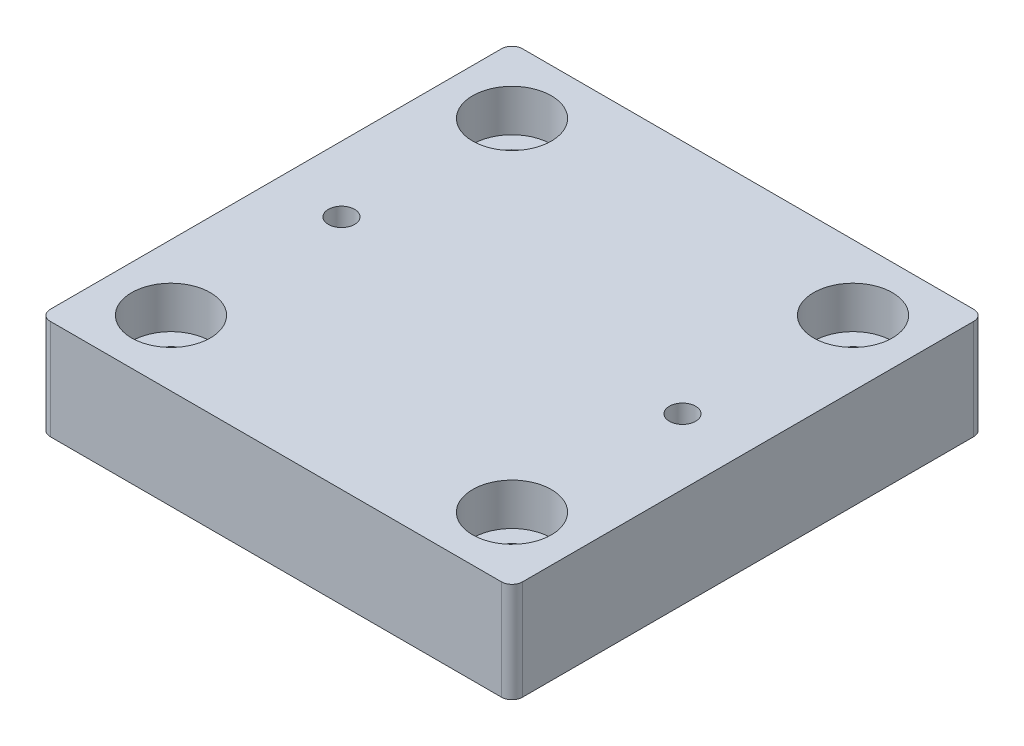
SolidWorks part; units mm, degrees
material "Plain Carbon Steel"
ref_plane "Front Plane" through (0, 0, 0) normal (0, 0, 1) x (1, 0, 0)
ref_plane "Top Plane" through (0, 0, 0) normal (0, 1, 0) x (1, 0, 0)
ref_plane "Right Plane" through (0, 0, 0) normal (1, 0, 0) x (0, 0, -1)
sketch "Sketch1" plane through (0, 0, 0) normal (0, 1, 0) x (1, 0, 0)
  line L0 (-32.5, 32.5) -> (-32.5, -32.5) construction
  line L1 (-43, -45) -> (43, -45)
  line L2 (-45, -43) -> (-45, 43)
  line L3 (-43, 45) -> (43, 45)
  line L4 (45, -43) -> (45, 43)
  line L5 (32.5, 32.5) -> (32.5, -32.5) construction
  arc A0 (-43, -45) -> (-45, -43) centre (-43, -43) cw
  arc A1 (43, -45) -> (45, -43) centre (43, -43) ccw
  arc A2 (43, 45) -> (45, 43) centre (43, 43) cw
  arc A3 (-45, 43) -> (-43, 45) centre (-43, 43) cw
  circle A4 centre (-32.5, 32.5) radius 12.5 construction
  circle A5 centre (-32.5, -32.5) radius 12.5 construction
  circle A6 centre (32.5, -32.5) radius 12.5 construction
  circle A7 centre (32.5, 32.5) radius 12.5 construction
  circle A8 centre (-32.5, 32.5) radius 4
  circle A9 centre (32.5, 32.5) radius 4
  circle A10 centre (32.5, -32.5) radius 4
  circle A11 centre (-32.5, -32.5) radius 4
  circle A12 centre (-32.5, 32.5) radius 7.5 construction
  circle A13 centre (32.5, 32.5) radius 7.5 construction
  circle A14 centre (-32.5, -32.5) radius 7.5 construction
  circle A15 centre (32.5, -32.5) radius 7.5 construction
  circle A16 centre (-32.5, 0) radius 3 construction
  circle A17 centre (32.5, 0) radius 3 construction
  point P0 (0, 0)
  point P2 (0, 45)
  point P3 (-45, 0)
  dimension "D1" = 2
  dimension "D4" = 15
  dimension "D6" = 8
  dimension "D7" = 6
  dimension "D2" = 90
  dimension "D3" = 90
  dimension "D5" = 65
extrude "Boss-Extrude1" add sketch "Sketch1" along normal blind 19.05
sketch "Sketch2" plane through (0, 19.05, 0) normal (0, 1, 0) x (1, 0, 0)
  circle A0 centre (-32.5, -32.5) radius 7.5 construction
  circle A1 centre (32.5, -32.5) radius 7.5 construction
  circle A2 centre (32.5, 32.5) radius 7.5 construction
  circle A3 centre (-32.5, 32.5) radius 7.5 construction
  circle A4 centre (-32.5, -32.5) radius 7.5
  circle A5 centre (32.5, -32.5) radius 7.5
  circle A6 centre (32.5, 32.5) radius 7.5
  circle A7 centre (-32.5, 32.5) radius 7.5
extrude "Cut-Extrude1" cut sketch "Sketch2" against normal blind 8
sketch "Sketch3" plane through (0, 19.05, 0) normal (0, 1, 0) x (1, 0, 0)
  line L0 (-32.5, 32.5) -> (-32.5, -32.5) construction
  line L1 (32.5, 32.5) -> (32.5, -32.5) construction
  point P0 (-32.5, 0)
  point P4 (32.5, 0)
hole_wizard "M6x1.0 Tapped Hole1" positions "Sketch3" profile "Sketch4" tap size "M6x1.0" standard "ANSI Metric" end condition through all
sketch "Sketch4" plane through (-32.5, 19.05, 0) normal (1, 0, 0) x (0, 0, 1)
  line L0 (0, 0) -> (0, 19.05)
  line L1 (0, 19.05) -> (2.5, 19.05)
  line L2 (2.5, 19.05) -> (2.5, 0)
  line L5 (2.5, 0) -> (0, 0)
  line L11 (0, -6.35) -> (0, 107.95) construction
  dimension "Thru Tap Drill Dia." = 5
  dimension "Thru Tap Drill Depth" = 19.05
cosmetic thread "Hole Thread1" parameters "D2"=6
cosmetic thread "Hole Thread2" parameters "D2"=6
equation "\"D3@Sketch1\"=\"D2@Sketch1\""
